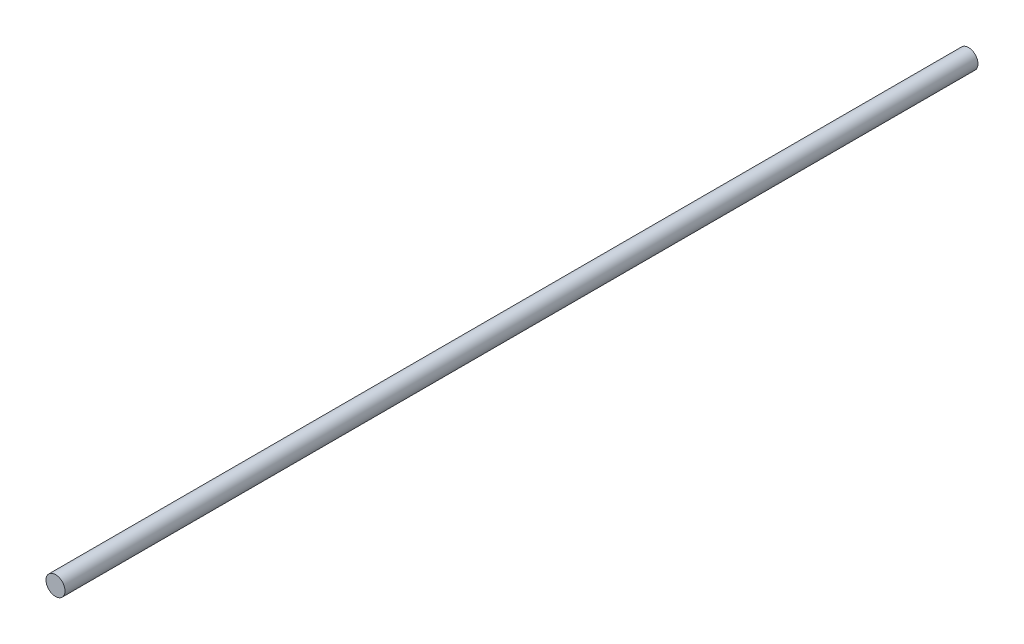
SolidWorks part; units mm, degrees
ref_plane "Front Plane" through (0, 0, 0) normal (0, 0, 1) x (1, 0, 0)
ref_plane "Top Plane" through (0, 0, 0) normal (0, 1, 0) x (1, 0, 0)
ref_plane "Right Plane" through (0, 0, 0) normal (1, 0, 0) x (0, 0, -1)
sketch "Sketch1" plane through (0, 0, 0) normal (0, 0, 1) x (1, 0, 0)
  circle A0 centre (0, 0) radius 3.175
  dimension "D1" = 6.35
extrude "Boss-Extrude1" add sketch "Sketch1" along normal mid plane 304.8
